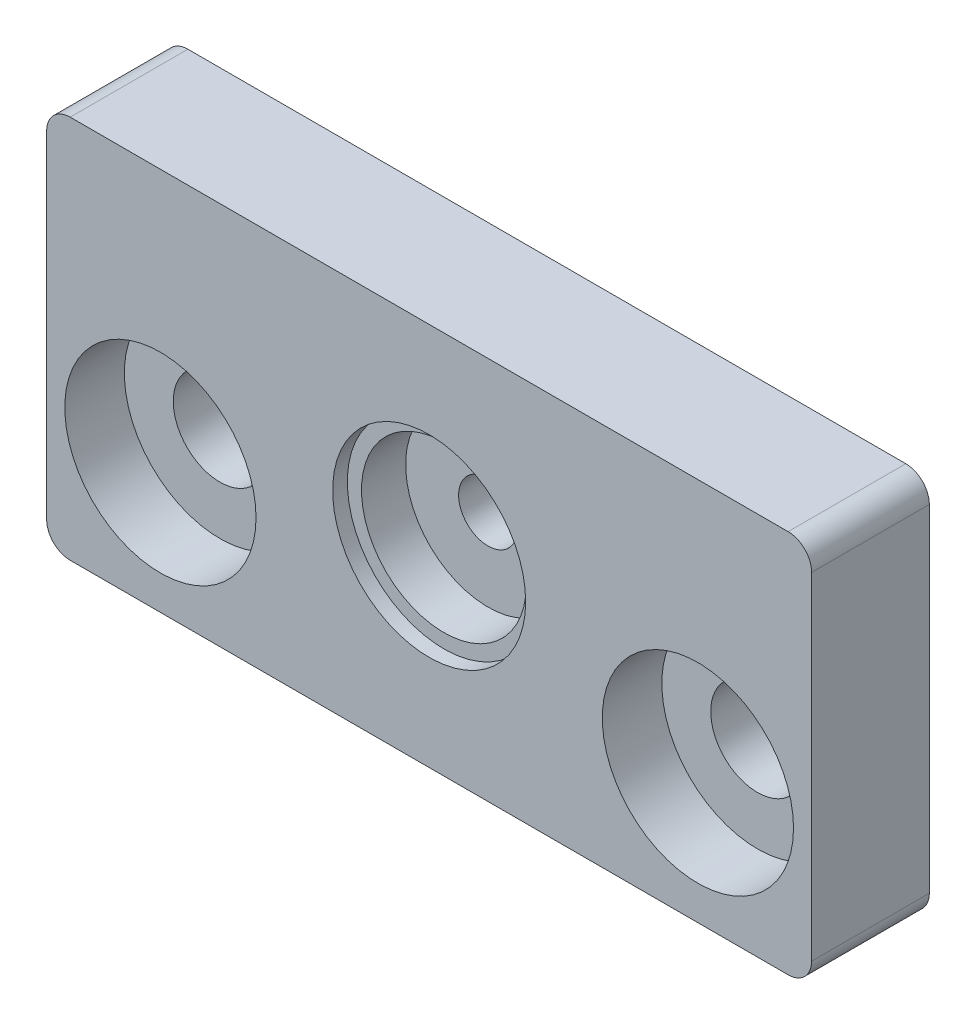
SolidWorks part; units mm, degrees
ref_plane "Front Plane" through (0, 0, 0) normal (0, 0, 1) x (1, 0, 0)
ref_plane "Top Plane" through (0, 0, 0) normal (0, 1, 0) x (1, 0, 0)
ref_plane "Right Plane" through (0, 0, 0) normal (1, 0, 0) x (0, 0, -1)
sketch "Sketch1" plane through (0, 0, 0) normal (0, 0, 1) x (1, 0, 0)
  line L1 (-41.275, -20.7073) -> (41.275, -20.7073)
  line L2 (-41.275, -20.7073) -> (-41.275, 20.7074)
  line L3 (-41.275, 20.7074) -> (41.275, 20.7074)
  line L4 (41.275, -20.7073) -> (41.275, 20.7074)
  line L5 (-41.275, -20.7073) -> (41.275, 20.7074) construction
  line L6 (-41.275, 20.7074) -> (41.275, -20.7073) construction
  point P0 (0, 0)
  dimension "D1" = 41.4147
  dimension "D2" = 82.55
extrude "Boss-Extrude1" add sketch "Sketch1" along normal blind 12.7
sketch "Sketch2" plane through (0, 0, 12.7) normal (0, 0, 1) x (1, 0, 0)
  line L0 (-41.275, 20.7074) -> (41.275, -20.7073) construction
  circle A0 centre (0, 0) radius 3.175
  dimension "D1" = 6.35
extrude "Cut-Extrude1" cut sketch "Sketch2" against normal blind 12.7
sketch "Sketch3" plane through (0, 0, 12.7) normal (0, 0, 1) x (1, 0, 0)
  circle A0 centre (0, 0) radius 8.89
  dimension "D1" = 17.78
extrude "Cut-Extrude2" cut sketch "Sketch3" against normal blind 6.35
sketch "Sketch5" plane through (0, 0, 12.7) normal (0, 0, 1) x (1, 0, 0)
  circle A0 centre (0, 0) radius 10.414
  dimension "D1" = 20.828
extrude "Cut-Extrude7" cut sketch "Sketch5" against normal blind 1.5875
fillet "Fillet1" radius 2.54 4 edges at (41.275, -20.7073, 6.35) (-41.275, -20.7073, 6.35) (-41.275, 20.7074, 6.35) (41.275, 20.7074, 6.35)
hole_wizard "CBORE for 3/8 Binding Head Machine Screw1" positions "Sketch8" profile "Sketch9" counterbore size "3/8" standard "ANSI Inch" end condition through all
sketch "Sketch8" plane through (0, 0, 12.7) normal (0, 0, 1) x (1, 0, 0)
  line L0 (0, 0) -> (0, -6.708) construction
  line L2 (0, -6.708) -> (29, -6.708) construction
  line L3 (0, -6.708) -> (-29, -6.708) construction
  circle A0 centre (0, 0) radius 3.175 construction
  point P9 (29, -6.708)
  point P11 (-29, -6.708)
  dimension "D1" = 6.708
  dimension "D2" = 29
  dimension "D3" = 29
sketch "Sketch9" plane through (-29, -6.708, 12.7) normal (1, 0, 0) x (0, -1, 0)
  line L0 (0, 0) -> (0, 12.7)
  line L1 (0, 12.7) -> (5.0419, 12.7)
  line L3 (5.0419, 12.7) -> (5.0419, 6.4262)
  line L4 (5.0419, 6.4262) -> (10.3187, 6.4262)
  line L5 (10.3187, 6.4262) -> (10.3187, 0)
  line L7 (10.3187, 0) -> (0, 0)
  line L11 (0, -6.35) -> (0, 107.95) construction
  dimension "Thru Hole Dia." = 10.0838
  dimension "Thru Hole Depth" = 12.7
  dimension "C'Bore Dia." = 20.6375
  dimension "C'Bore Depth" = 6.4262
